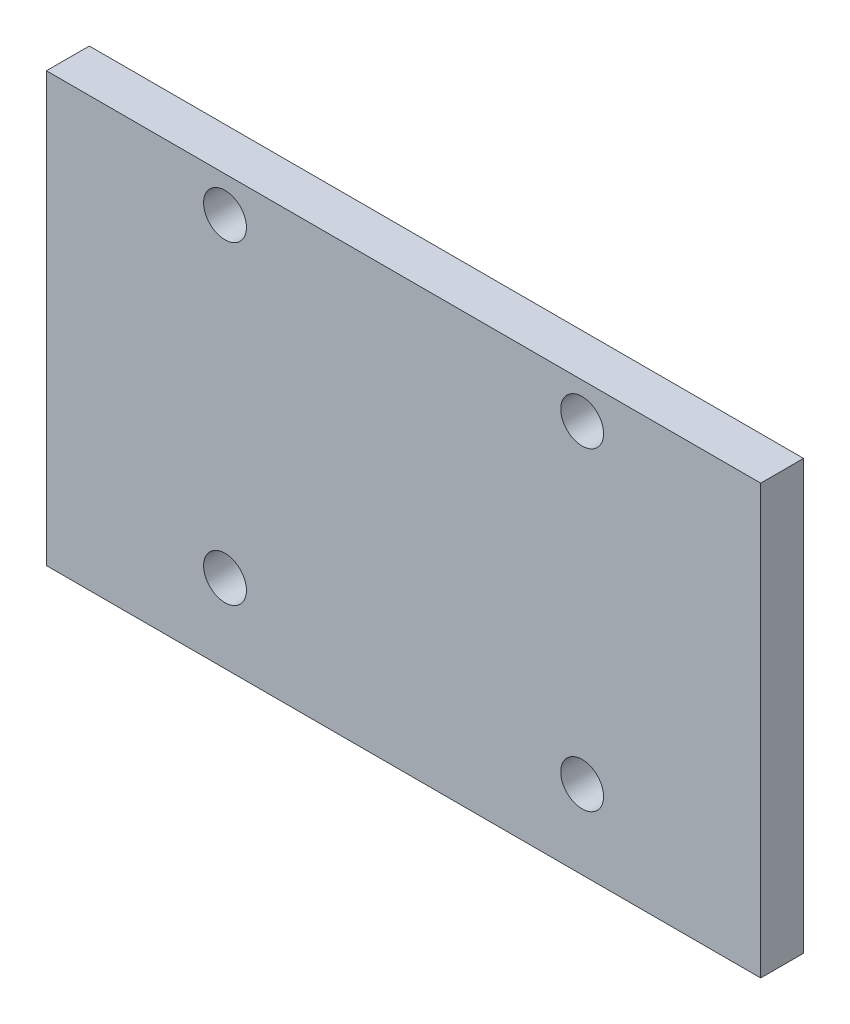
SolidWorks part; units mm, degrees
ref_plane "Plan de face" through (0, 0, 0) normal (0, 0, 1) x (1, 0, 0)
ref_plane "Plan de dessus" through (0, 0, 0) normal (0, 1, 0) x (1, 0, 0)
ref_plane "Plan de droite" through (0, 0, 0) normal (1, 0, 0) x (0, 0, -1)
sketch "Esquisse1" plane through (0, 0, 0) normal (0, 0, 1) x (1, 0, 0)
  line L1 (-30.8602, 15.5642) -> (19.1398, 15.5642)
  line L2 (-30.8602, 15.5642) -> (-30.8602, -14.4358)
  line L3 (-30.8602, -14.4358) -> (19.1398, -14.4358)
  line L4 (19.1398, 15.5642) -> (19.1398, -14.4358)
  circle A0 centre (-18.3602, 13.0642) radius 1.5
  circle A1 centre (6.6398, 13.0642) radius 1.5
  circle A2 centre (-18.3602, -8.9358) radius 1.5
  circle A3 centre (6.6398, -8.9358) radius 1.5
  dimension "D3" = 12.5
  dimension "D1" = 50
  dimension "D2" = 30
  dimension "D4" = 12.5
  dimension "D5" = 12.5
  dimension "D6" = 12.5
  dimension "D7" = 2.5
  dimension "D8" = 2.5
  dimension "D9" = 5.5
  dimension "D10" = 5.5
extrude "Boss.-Extru.1" add sketch "Esquisse1" along normal blind 3
